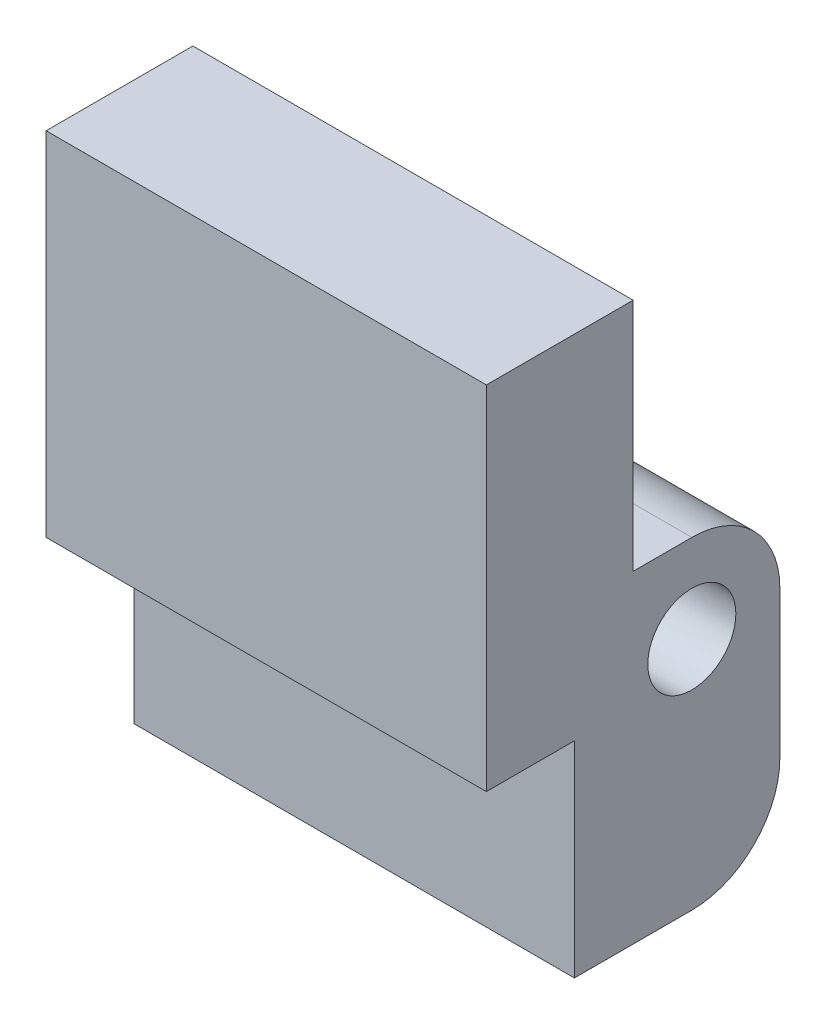
SolidWorks part; units mm, degrees
ref_plane "Front Plane" through (0, 0, 0) normal (0, 0, 1) x (1, 0, 0)
ref_plane "Top Plane" through (0, 0, 0) normal (0, 1, 0) x (1, 0, 0)
ref_plane "Right Plane" through (0, 0, 0) normal (1, 0, 0) x (0, 0, -1)
sketch "Sketch1" plane through (0, 0, 0) normal (1, 0, 0) x (0, 0, -1)
  line L1 (-2.1479, 5.1268) -> (2.8521, 5.1268)
  line L2 (-2.1479, 5.1268) -> (-2.1479, -6.8732)
  line L3 (-2.1479, -6.8732) -> (0.8521, -6.8732)
  line L4 (2.8521, 5.1268) -> (2.8521, -2.8732)
  line L5 (2.8521, -2.8732) -> (4.8521, -2.8732)
  line L6 (0.8521, -6.8732) -> (0.8521, -13.8732)
  line L7 (0.8521, -13.8732) -> (4.8521, -13.8732)
  line L8 (7.8521, -5.8732) -> (7.8521, -10.8732)
  arc A0 (4.8521, -13.8732) -> (7.8521, -10.8732) centre (4.8521, -10.8732) ccw
  arc A1 (4.8521, -2.8732) -> (7.8521, -5.8732) centre (4.8521, -5.8732) cw
  circle A2 centre (4.8521, -5.8732) radius 1.5
  point P14 (4.8521, -5.6256)
  dimension "D5" = 3
  dimension "D8" = 3
  dimension "D9" = 3
  dimension "D1" = 5
  dimension "D2" = 8
  dimension "D3" = 5
  dimension "D4" = 3
  dimension "D6" = 4
  dimension "D7" = 11
extrude "Boss-Extrude1" add sketch "Sketch1" along normal blind 15
